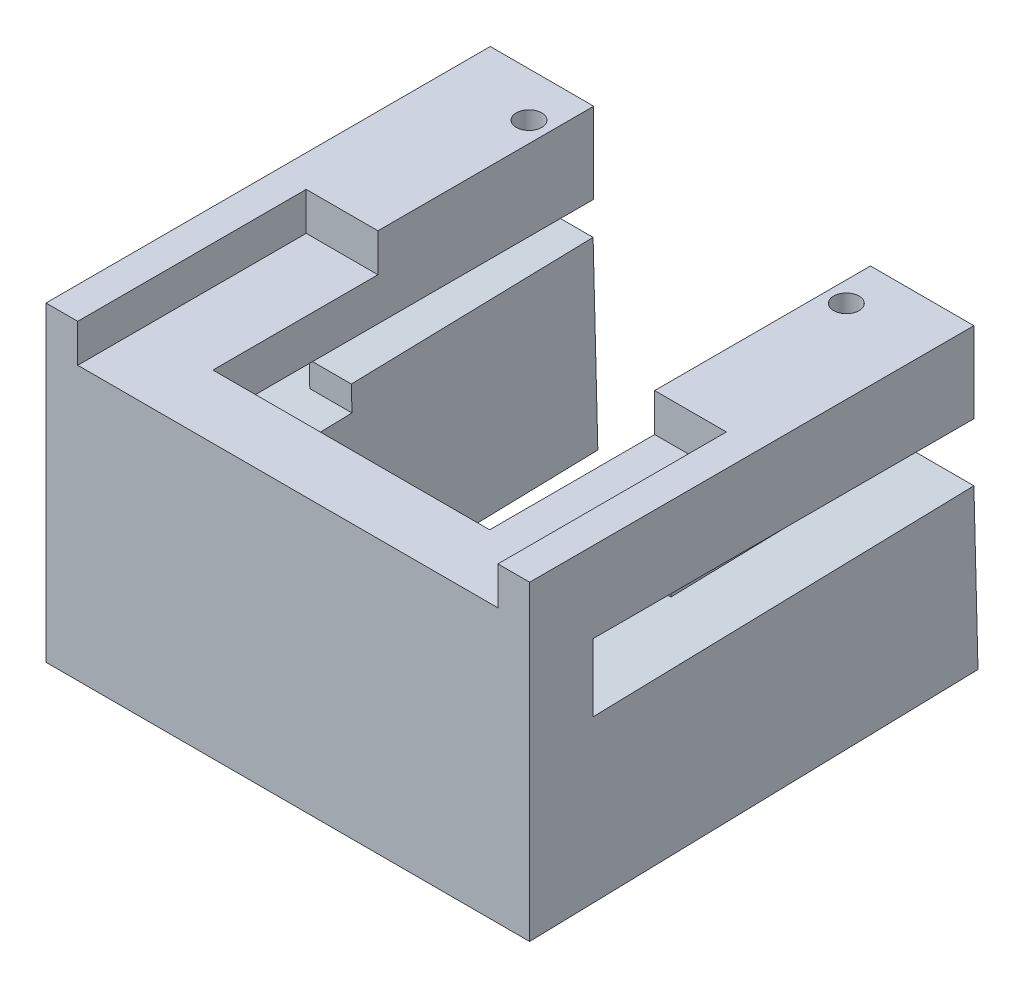
SolidWorks part; units mm, degrees
ref_plane "Front Plane" through (0, 0, 0) normal (0, 0, 1) x (1, 0, 0)
ref_plane "Top Plane" through (0, 0, 0) normal (0, 1, 0) x (1, 0, 0)
ref_plane "Right Plane" through (0, 0, 0) normal (1, 0, 0) x (0, 0, -1)
sketch "Sketch1" plane through (0, 0, 0) normal (1, 0, 0) x (0, 0, -1)
  line L0 (0, 7.406) -> (0, -7.406)
  line L1 (0, -7.406) -> (35.0762, -6.515)
  line L2 (35.0762, -6.515) -> (35, -3.516)
  line L3 (35, -3.516) -> (5, -4.278)
  line L4 (5, -4.278) -> (5, 1.056)
  line L5 (5, 1.056) -> (35, 1.056)
  line L6 (35, 1.056) -> (35, 7.406)
  line L7 (35, 7.406) -> (0, 7.406)
  line L8 (0, -7.406) -> (0, -17.1091)
  line L9 (0, -17.1091) -> (35.3225, -16.2119)
  line L10 (35.3225, -16.2119) -> (35.0762, -6.515)
  point P4 (0, 0)
  dimension "D1" = 5.334
  dimension "D2" = 4.572
  dimension "D3" = 3
  dimension "D4" = 5
  dimension "D5" = 6.35
  dimension "D6" = 35
  dimension "D7" = 12.7
extrude "Boss-Extrude1" add sketch "Sketch1" along normal mid plane 38.1 contours L6 L7 L0 L1 L2 L3 L4 L5 | L9 L10 L1 L8
sketch "Sketch2" plane through (0, 7.406, 0) normal (0, 1, 0) x (1, 0, 0)
  line L0 (-12.5, 31.5) -> (12.5, 31.5) construction
  line L1 (0, 31.5) -> (0, 35) construction
  line L2 (19.05, 35) -> (-19.05, 35) construction
  line L3 (0, 35) -> (0, 31.5) construction
  line L4 (-10.9, 37.9788) -> (10.9, 37.9788)
  line L5 (-10.9, 37.9788) -> (-10.9, 5)
  line L6 (-10.9, 5) -> (10.9, 5)
  line L7 (10.9, 37.9788) -> (10.9, 5)
  circle A0 centre (-12.5, 31.5) radius 1
  circle A1 centre (12.5, 31.5) radius 1
  point P12 (0, 37.9788)
  dimension "D1" = 2
  dimension "D2" = 25
  dimension "D3" = 3.5
  dimension "D4" = 21.8
extrude "Cut-Extrude1" cut sketch "Sketch2" against normal through all
sketch "Sketch3" plane through (0, 7.406, 0) normal (0, 1, 0) x (1, 0, 0)
  line L1 (-16.55, 18) -> (16.55, 18)
  line L2 (-16.55, 18) -> (-16.55, 0)
  line L3 (-16.55, 0) -> (16.55, 0)
  line L4 (16.55, 18) -> (16.55, 0)
  line L5 (0, 18) -> (0, 0) construction
  line L6 (19.05, 0) -> (-19.05, 0) construction
  line L9 (-19.05, 35) -> (-19.05, 0) construction
  dimension "D1" = 2.5
  dimension "D2" = 18
extrude "Cut-Extrude2" cut sketch "Sketch3" against normal blind 3
sketch "Sketch4" plane through (0, -4.4022, -0.1118) normal (0, 0.9997, 0.0254) x (1, 0, 0)
  line L1 (14.224, 34.8994) -> (10.9, 34.8994)
  line L2 (14.224, 34.8994) -> (14.224, 15.8494)
  line L3 (14.224, 15.8494) -> (10.9, 15.8494)
  line L4 (10.9, 34.8994) -> (10.9, 15.8494)
  line L5 (-14.224, 15.8494) -> (-10.9, 15.8494)
  line L6 (-14.224, 15.8494) -> (-14.224, 34.8994)
  line L7 (-14.224, 34.8994) -> (-10.9, 34.8994)
  line L8 (-10.9, 15.8494) -> (-10.9, 34.8994)
  line L9 (-10.9, 34.8994) -> (-19.05, 34.8994) construction
  line L10 (19.05, 34.8994) -> (10.9, 34.8994) construction
  dimension "D1" = 28.448
  dimension "D2" = 19.05
extrude "Boss-Extrude2" add sketch "Sketch4" along normal blind 2 and the other way up to surface (12.7 mm away) other way up to face at (-12.5, -16.2836, -32.5)
